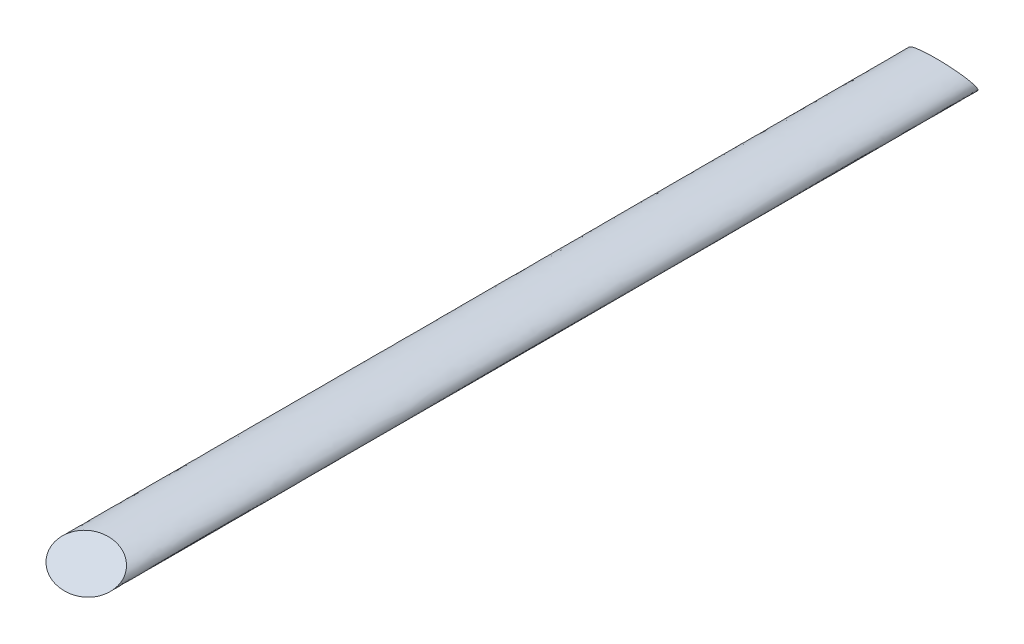
SolidWorks part; units mm, degrees
ref_plane "Front Plane" through (0, 0, 0) normal (0, 0, 1) x (1, 0, 0)
ref_plane "Top Plane" through (0, 0, 0) normal (0, 1, 0) x (1, 0, 0)
ref_plane "Right Plane" through (0, 0, 0) normal (1, 0, 0) x (0, 0, -1)
sketch "Sketch1" plane through (0, 0, 0) normal (0, 0, 1) x (1, 0, 0)
  ellipse E0 centre (0, 0) end of major axis (67.7799, 0) minor radius 25.3619
  dimension "D1" = 67.7799
  dimension "D2" = 25.3619
extrude "Boss-Extrude2" add sketch "Sketch1" along normal blind 1778
sketch "Sketch2" plane through (0, 0, 0) normal (1, 0, 0) x (0, 0, -1)
  line L0 (-1778, -25.3619) -> (-1645.9683, 50.8667)
  line L1 (-1645.9683, 50.8667) -> (-2758.2744, 50.8667)
  line L2 (-2758.2744, 50.8667) -> (-2758.2744, -25.3619)
  line L3 (-2758.2744, -25.3619) -> (-1778, -25.3619)
  line L4 (0, -25.3619) -> (-29.2854, 25.3619)
  line L5 (0, 25.3619) -> (-1778, 25.3619) construction
  line L6 (-29.2854, 25.3619) -> (0, 25.3619)
  line L7 (0, 25.3619) -> (0, -25.3619)
extrude "Cut-Extrude1" cut sketch "Sketch2" against normal through all and the other way through all
